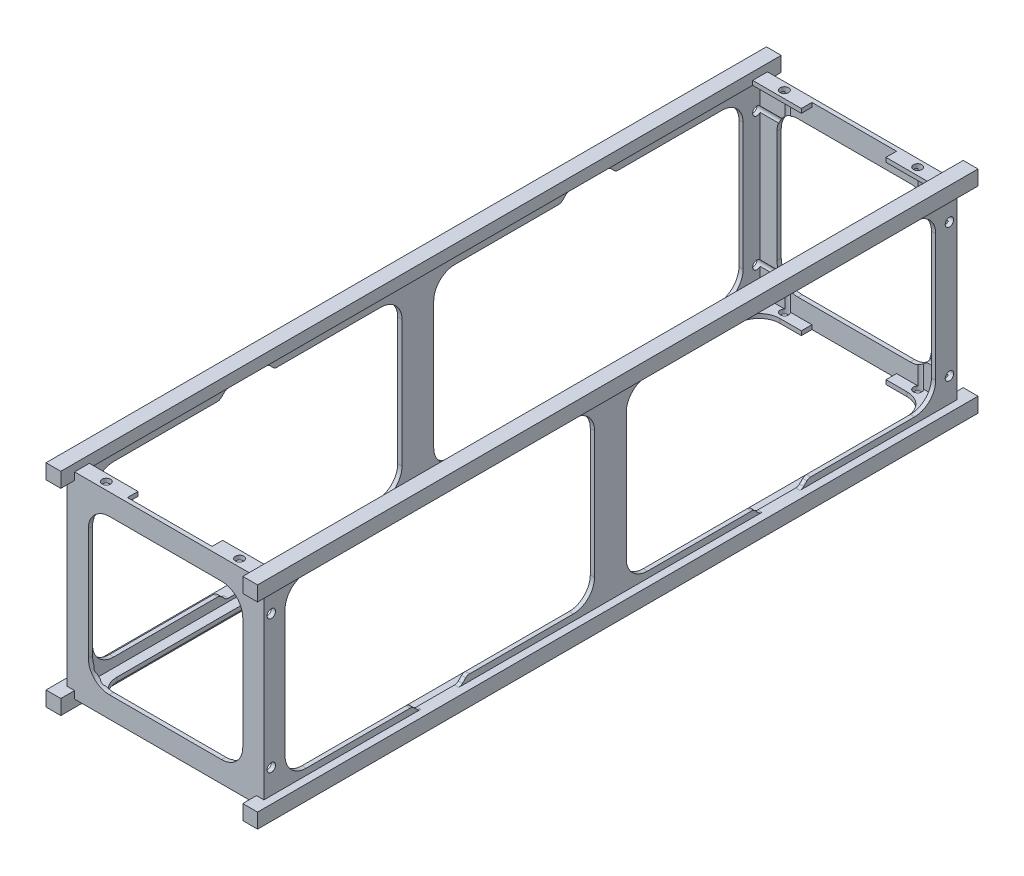
SolidWorks part; units mm, degrees
ref_plane "Front Plane" through (0, 0, 0) normal (0, 0, 1) x (1, 0, 0)
ref_plane "Top Plane" through (0, 0, 0) normal (0, 1, 0) x (1, 0, 0)
ref_plane "Right Plane" through (0, 0, 0) normal (1, 0, 0) x (0, 0, -1)
sketch "Sketch1" plane through (0, 0, 0) normal (0, 0, 1) x (1, 0, 0)
  line L1 (0, 0) -> (10, 0)
  line L2 (0, 0) -> (0, 10)
  line L3 (0, 10) -> (10, 10)
  line L4 (10, 0) -> (10, 10)
extrude "Rail profile" add sketch "Sketch1" along normal blind 34.05
sketch "Sketch2" plane through (0, 0, 0) normal (0, 0, -1) x (-1, 0, 0)
  line L0 (-10, 9.3) -> (-10, 0.7)
  line L3 (-10, 9.3) -> (-9.3, 9.3)
  line L4 (-9.3, 10) -> (-9.3, 9.3)
  line L7 (-10, 0.7) -> (-9.3, 0.7)
  line L8 (-9.3, 0) -> (-9.3, 0.7)
  line L11 (0, 0.7) -> (-0.7, 0.7)
  line L12 (-0.7, 0) -> (-0.7, 0.7)
  line L15 (0, 9.3) -> (-0.7, 9.3)
  line L16 (-0.7, 10) -> (-0.7, 9.3)
  line L17 (-9.3, 10) -> (-0.7, 10)
  line L18 (0, 9.3) -> (0, 0.7)
  line L19 (-0.7, 0) -> (-9.3, 0)
extrude "Rails thickness" cut sketch "Sketch2" against normal up to surface (34.05 mm away) contours L8 L7 L0 L3 L4 L17 L16 L15 L18 L11 L12 L19 up to face at (5, 5, 34.05)
ref_plane "Wall plane" through (0, 0, 0.65) normal (0, 0, -1) x (-1, 0, 0)
ref_plane "Wall plane 2" through (0, 0, 33.4) normal (0, 0, 1) x (1, 0, 0)
sketch "Sketch4" plane through (0, 0, 0.65) normal (0, 0, -1) x (-1, 0, 0)
  line L0 (-9.3, 9.65) -> (-9.3, 9.3)
  line L5 (-9.3, 9.3) -> (-9.65, 9.3)
  line L6 (-0.7, 9.65) -> (-0.7, 9.3)
  line L7 (-0.7, 9.3) -> (-0.35, 9.3)
  line L8 (-0.7, 0.35) -> (-0.7, 0.7)
  line L9 (-0.7, 0.7) -> (-0.35, 0.7)
  line L10 (-9.3, 0.35) -> (-9.3, 0.7)
  line L11 (-9.3, 0.7) -> (-9.65, 0.7)
  line L12 (-9.3, 9.65) -> (-0.7, 9.65)
  line L13 (-0.35, 9.3) -> (-0.35, 0.7)
  line L14 (-0.7, 0.35) -> (-9.3, 0.35)
  line L15 (-9.65, 0.7) -> (-9.65, 9.3)
  line L16 (-9.3, 10) -> (-9.3, 9.3) construction
  line L19 (-9.3, 0) -> (-9.3, 0.7) construction
  line L20 (-10, 0.7) -> (-9.3, 0.7) construction
  line L21 (-10, 9.3) -> (-9.3, 9.3) construction
  line L22 (-0.7, 0) -> (-0.7, 0.7) construction
  line L25 (0, 9.3) -> (-0.7, 9.3) construction
extrude "Walls" add sketch "Sketch4" against normal up to surface (32.75 mm away) up to plane "Wall plane 2"
sketch "Sketch7" plane through (0, 0, 0.65) normal (0, 0, -1) x (-1, 0, 0)
  line L0 (-5, 9.65) -> (-5, 8.65) construction
  line L1 (-7.65, 8.65) -> (-2.35, 8.65)
  line L2 (-8.65, 7.65) -> (-8.65, 2.35)
  line L3 (-7.65, 1.35) -> (-2.35, 1.35)
  line L4 (-1.35, 7.65) -> (-1.35, 2.35)
  line L5 (-0.7, 9.65) -> (-9.3, 9.65) construction
  line L6 (-8.65, 5) -> (-9.65, 5) construction
  line L8 (-9.65, 9.3) -> (-9.65, 0.7) construction
  arc A0 (-8.65, 2.35) -> (-7.65, 1.35) centre (-7.65, 2.35) ccw
  arc A1 (-2.35, 1.35) -> (-1.35, 2.35) centre (-2.35, 2.35) ccw
  arc A2 (-2.35, 8.65) -> (-1.35, 7.65) centre (-2.35, 7.65) cw
  arc A3 (-7.65, 8.65) -> (-8.65, 7.65) centre (-7.65, 7.65) ccw
  dimension "D1" = 1
extrude "Hole in square wall" cut sketch "Sketch7" against normal up to surface (32.75 mm away) up to face at (5, 5, 33.4)
sketch "Sketch9" plane through (0, 9.65, 0) normal (0, 1, 0) x (1, 0, 0)
  line L0 (0.7, -0.65) -> (0.7, -0.85) construction
  line L1 (0.7, -34.05) -> (0.7, 0) construction
  line L2 (5, -0.85) -> (5, -1.35) construction
  line L4 (5, -1.35) -> (3, -1.35) construction
  line L5 (5, -1.35) -> (5, -17.025) construction
  line L6 (9.3, -33.2) -> (9.3, -33.4) construction
  line L7 (9.3, -33.4) -> (9.3, -0.65) construction
  line L8 (-0.385, -33.4) -> (0.385, -33.4) construction
  line L9 (3, -1.35) -> (3, -0.85)
  line L11 (3, -1.35) -> (2, -1.35)
  line L12 (9, -2.35) -> (9, -31.7)
  line L14 (1, -1.35) -> (0, -1.35) construction
  line L17 (7, -0.85) -> (3, -0.85)
  line L19 (1, -31.7) -> (1, -2.35)
  line L20 (0, -34.05) -> (0, 0) construction
  line L33 (7, -1.35) -> (8, -1.35)
  line L34 (7, -1.35) -> (7, -0.85)
  line L35 (3, -32.7) -> (2, -32.7)
  line L36 (3, -32.7) -> (3, -33.2)
  line L49 (7, -32.7) -> (8, -32.7)
  line L50 (7, -32.7) -> (7, -33.2)
  line L51 (7, -33.2) -> (3, -33.2)
  arc A0 (1, -2.35) -> (2, -1.35) centre (2, -2.35) cw
  arc A9 (9, -2.35) -> (8, -1.35) centre (8, -2.35) ccw
  arc A10 (1, -31.7) -> (2, -32.7) centre (2, -31.7) ccw
  arc A19 (9, -31.7) -> (8, -32.7) centre (8, -31.7) cw
  point P41 (1, -10.6125)
  point P44 (1, -7.7625)
  point P53 (9, -10.6125)
  point P61 (9, -7.7625)
  point P62 (9, -26.2875)
  point P81 (1, -26.2875)
  point P89 (1, -23.4375)
  point P90 (1, -17.025)
  point P105 (9, -17.025)
  point P106 (9, -23.4375)
  dimension "D1" = 1
extrude "Hole in long wall" cut sketch "Sketch9" against normal up to surface (9.3 mm away) up to face at (5, 0.35, 17.025)
sketch "Sketch14" plane through (9.65, 0, 0) normal (1, 0, 0) x (0, 0, -1)
  line L0 (-33.4, 10) -> (-33.4, 9) construction
  line L1 (-34.05, 10) -> (0, 10) construction
  line L2 (-33.4, 9.3) -> (-33.4, 0.7) construction
  line L3 (-33.4, 9) -> (-32.4, 9) construction
  line L4 (-25.0875, 9) -> (-25.0875, 10.2139) construction
  line L5 (-18.775, 1) -> (-23.6839, 1)
  line L6 (-0.65, 9.3) -> (-0.65, 0.7) construction
  line L7 (-0.65, 1) -> (-1.65, 1) construction
  line L8 (-17.025, 9) -> (-17.025, 1) construction
  line L12 (-32.4, 2) -> (-32.4, 8)
  line L13 (-25.9839, 9.3) -> (-25.0875, 9.3)
  line L14 (-33.4, 9.3) -> (-0.65, 9.3) construction
  line L15 (-17.775, 2) -> (-17.775, 8)
  line L16 (-18.775, 9) -> (-23.6839, 9)
  line L17 (-34.05, 9.3) -> (0, 9.3) construction
  line L18 (-25.0875, 9.3) -> (-24.1911, 9.3)
  line L19 (-24.0143, 9.2268) -> (-23.8607, 9.0732)
  line L20 (-26.1607, 9.2268) -> (-26.3143, 9.0732)
  line L21 (-26.4911, 9) -> (-31.4, 9)
  line L22 (-32.4, 5) -> (-17.775, 5) construction
  line L23 (-25.0875, 1) -> (-25.0875, -0.2139) construction
  line L24 (-26.4911, 1) -> (-31.4, 1)
  line L25 (-26.1607, 0.7732) -> (-26.3143, 0.9268)
  line L26 (-24.0143, 0.7732) -> (-23.8607, 0.9268)
  line L27 (-25.0875, 0.7) -> (-24.1911, 0.7)
  line L28 (-25.9839, 0.7) -> (-25.0875, 0.7)
  line L29 (-16.275, 2) -> (-16.275, 8)
  line L30 (-15.275, 9) -> (-10.3661, 9)
  line L31 (-10.0357, 9.2268) -> (-10.1893, 9.0732)
  line L32 (-8.9625, 9.3) -> (-9.8589, 9.3)
  line L33 (-8.0661, 9.3) -> (-8.9625, 9.3)
  line L34 (-7.8893, 9.2268) -> (-7.7357, 9.0732)
  line L35 (-7.5589, 9) -> (-2.65, 9)
  line L36 (-1.65, 2) -> (-1.65, 8)
  line L37 (-7.5589, 1) -> (-2.65, 1)
  line L38 (-7.8893, 0.7732) -> (-7.7357, 0.9268)
  line L39 (-8.0661, 0.7) -> (-8.9625, 0.7)
  line L40 (-8.9625, 0.7) -> (-9.8589, 0.7)
  line L41 (-10.0357, 0.7732) -> (-10.1893, 0.9268)
  line L42 (-15.275, 1) -> (-10.3661, 1)
  arc A3 (-32.4, 8) -> (-31.4, 9) centre (-31.4, 8) cw
  arc A5 (-18.775, 9) -> (-17.775, 8) centre (-18.775, 8) cw
  arc A6 (-23.8607, 9.0732) -> (-23.6839, 9) centre (-23.6839, 9.25) ccw
  arc A7 (-24.1911, 9.3) -> (-24.0143, 9.2268) centre (-24.1911, 9.05) cw
  arc A8 (-25.9839, 9.3) -> (-26.1607, 9.2268) centre (-25.9839, 9.05) ccw
  arc A9 (-26.3143, 9.0732) -> (-26.4911, 9) centre (-26.4911, 9.25) cw
  arc A10 (-26.3143, 0.9268) -> (-26.4911, 1) centre (-26.4911, 0.75) ccw
  arc A11 (-25.9839, 0.7) -> (-26.1607, 0.7732) centre (-25.9839, 0.95) cw
  arc A12 (-24.1911, 0.7) -> (-24.0143, 0.7732) centre (-24.1911, 0.95) ccw
  arc A13 (-23.8607, 0.9268) -> (-23.6839, 1) centre (-23.6839, 0.75) cw
  arc A14 (-18.775, 1) -> (-17.775, 2) centre (-18.775, 2) ccw
  arc A15 (-32.4, 2) -> (-31.4, 1) centre (-31.4, 2) ccw
  arc A16 (-15.275, 1) -> (-16.275, 2) centre (-15.275, 2) cw
  arc A17 (-15.275, 9) -> (-16.275, 8) centre (-15.275, 8) ccw
  arc A18 (-10.1893, 9.0732) -> (-10.3661, 9) centre (-10.3661, 9.25) cw
  arc A19 (-9.8589, 9.3) -> (-10.0357, 9.2268) centre (-9.8589, 9.05) ccw
  arc A20 (-8.0661, 9.3) -> (-7.8893, 9.2268) centre (-8.0661, 9.05) cw
  arc A21 (-7.7357, 9.0732) -> (-7.5589, 9) centre (-7.5589, 9.25) ccw
  arc A22 (-1.65, 8) -> (-2.65, 9) centre (-2.65, 8) ccw
  arc A23 (-1.65, 2) -> (-2.65, 1) centre (-2.65, 2) cw
  arc A24 (-7.7357, 0.9268) -> (-7.5589, 1) centre (-7.5589, 0.75) cw
  arc A25 (-8.0661, 0.7) -> (-7.8893, 0.7732) centre (-8.0661, 0.95) ccw
  arc A26 (-9.8589, 0.7) -> (-10.0357, 0.7732) centre (-9.8589, 0.95) cw
  arc A27 (-10.1893, 0.9268) -> (-10.3661, 1) centre (-10.3661, 0.75) ccw
  point P31 (-24.0875, 9.3)
  point P40 (-26.0875, 9.3)
  point P43 (-26.3875, 9)
  point P61 (-26.3875, 1)
  point P62 (-26.0875, 0.7)
  point P63 (-24.0875, 0.7)
  dimension "D1" = 0.25
extrude "Holes in loneg wall 2" cut sketch "Sketch14" against normal up to surface (9.3 mm away) up to face at (0.35, 5, 17.025)
ref_plane "Wall thickness Plane" through (0, 0, 0.85) normal (0, 0, -1) x (-1, 0, 0)
ref_plane "Wall thickness Plane 2" through (0, 0, 33.2) normal (0, 0, 1) x (1, 0, 0)
sketch "Sketch12" plane through (0, 0, 33.2) normal (0, 0, 1) x (1, 0, 0)
  line L0 (0.55, 9.65) -> (0.55, 9.45) construction
  line L1 (9.65, 9.3) -> (9.65, 0.7) construction
  line L2 (0.55, 9.45) -> (0.35, 9.45) construction
  line L4 (0.35, 9.45) -> (0.35, 9.65) construction
  line L5 (0.35, 9.65) -> (0.55, 9.65) construction
  line L6 (9.65, 0.35) -> (9.45, 0.35) construction
  line L8 (9.45, 0.35) -> (9.45, 0.55) construction
  line L9 (9.45, 0.55) -> (9.65, 0.55) construction
  line L11 (9.65, 0.55) -> (9.65, 0.35) construction
  line L13 (0.55, 9.45) -> (9.45, 9.45)
  line L14 (0.55, 9.45) -> (0.55, 0.55)
  line L15 (0.55, 0.55) -> (9.45, 0.55)
  line L16 (9.45, 9.45) -> (9.45, 0.55)
  line L20 (9.3, 0.35) -> (0.7, 0.35) construction
  line L22 (0.35, 0.7) -> (0.35, 9.3) construction
  line L23 (0.7, 9.65) -> (9.3, 9.65) construction
extrude "Create inner volume" cut sketch "Sketch12" against normal up to surface (32.35 mm away)
sketch "Sketch15" plane through (0, 9.65, 0) normal (0, 1, 0) x (1, 0, 0)
  line L0 (9.3, -1.35) -> (0.7, -1.35)
  line L1 (0.7, -34.05) -> (0.7, 0) construction
  line L2 (9.3, -33.4) -> (9.3, -0.65) construction
  line L3 (0.7, -1.35) -> (0.7, -32.7)
  line L4 (0.7, -33.4) -> (0.7, -0.65) construction
  line L5 (0.7, -32.7) -> (9.3, -32.7)
  line L6 (9.3, -32.7) -> (9.3, -1.35)
extrude "Cut to open one side" cut sketch "Sketch15" against normal up to surface (0.2 mm away) up to face at (8.1314, 9.45, 17.025)
sketch "Sketch16" plane through (0, 9.65, 0) normal (0, 1, 0) x (1, 0, 0)
  line L0 (1.85, -1.35) -> (1.85, -0.65) construction
  line L1 (3, -1.35) -> (0.7, -1.35) construction
  line L2 (0.7, -0.65) -> (9.3, -0.65) construction
  line L3 (5, -0.65) -> (5, -33.4) construction
  line L4 (0.7, -33.4) -> (9.3, -33.4) construction
  line L5 (0, -17.025) -> (10, -17.025) construction
  line L6 (0, -34.05) -> (0, 0) construction
  line L7 (10, -34.05) -> (10, 0) construction
  circle A0 centre (1.85, -1) radius 0.2
  circle A1 centre (8.15, -1) radius 0.2
  circle A2 centre (8.15, -33.05) radius 0.2
  circle A3 centre (1.85, -33.05) radius 0.2
extrude "Cut-Extrude2" cut sketch "Sketch16" against normal up to surface (9.3 mm away) up to face at (5, 0.35, 17.025)
sketch "Sketch17" plane through (9.65, 0, 0) normal (1, 0, 0) x (0, 0, -1)
  line L0 (-33.4, 8.15) -> (-33.05, 8.15) construction
  line L1 (-33.4, 9.3) -> (-33.4, 0.7) construction
  line L2 (-33.05, 9.3) -> (-33.05, 8.15) construction
  line L4 (-34.05, 9.3) -> (0, 9.3) construction
  line L5 (-17.025, 9.3) -> (-17.025, 0.7) construction
  line L6 (-24.1911, 0.7) -> (-9.8589, 0.7) construction
  line L7 (-33.4, 5) -> (-0.65, 5) construction
  line L8 (-0.65, 9.3) -> (-0.65, 0.7) construction
  circle A0 centre (-33.05, 8.15) radius 0.2
  circle A1 centre (-33.05, 1.85) radius 0.2
  circle A2 centre (-1, 1.85) radius 0.2
  circle A3 centre (-1, 8.15) radius 0.2
extrude "Cut-Extrude3" cut sketch "Sketch17" against normal up to surface (9.3 mm away) up to face at (0.35, 5, 5.1418)
scale "Scale1" bodies to scale 120 scale about centroid uniform scaling yes scale factor 10
